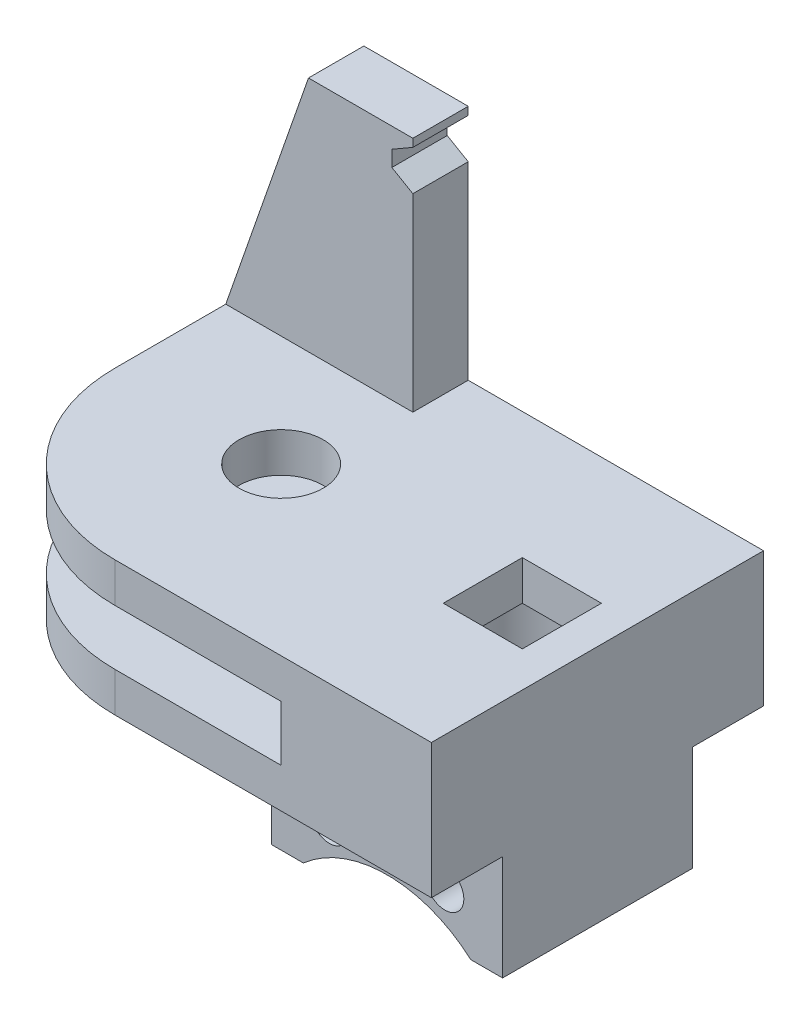
SolidWorks part; units mm, degrees
ref_plane "Front Plane" through (0, 0, 0) normal (0, 0, 1) x (1, 0, 0)
ref_plane "Top Plane" through (0, 0, 0) normal (0, 1, 0) x (1, 0, 0)
ref_plane "Right Plane" through (0, 0, 0) normal (1, 0, 0) x (0, 0, -1)
sketch "Sketch1" plane through (0, 0, 0) normal (0, 1, 0) x (1, 0, 0)
  line L0 (0, -13.335) -> (25.4, -13.335)
  line L1 (0, 13.335) -> (25.4, 13.335)
  line L2 (25.4, 13.335) -> (25.4, -13.335)
  circle A0 centre (0, 0) radius 12.7 construction
  circle A1 centre (0, 0) radius 13.335 construction
  circle A2 centre (0, 0) radius 3.3782
  arc A3 (11.5484, 6.6675) -> (11.5484, -6.6675) centre (0, 0) ccw construction
  arc A4 (0, 13.335) -> (0, -13.335) centre (0, 0) ccw
  dimension "D1" = 25.4
  dimension "D2" = 0.635
  dimension "D4" = 6.7564
  dimension "D3" = 25.4
extrude "Boss-Extrude1" add sketch "Sketch1" along normal blind 3.175
sketch "Sketch2" plane through (0, 0, 0) normal (0, -1, 0) x (-1, 0, 0)
  line L3 (-25.4, 13.335) -> (-25.4, -13.335)
  line L5 (-13.335, 0) -> (-13.335, 13.335)
  line L6 (-25.4, 13.335) -> (-13.335, 13.335)
  line L7 (-13.335, 0) -> (-13.335, -13.335)
  line L8 (0, -13.335) -> (-25.4, -13.335) construction
  line L9 (-13.335, -13.335) -> (-25.4, -13.335)
  arc A3 (0, 13.335) -> (0, -13.335) centre (0, 0) ccw construction
extrude "Boss-Extrude2" add sketch "Sketch2" along normal blind 4.445 contours L3 L9 L7 L5 L6
ref_plane "Plane2" through (0, -2.2225, 0) normal (0, -1, 0) x (-1, 0, 0)
mirror "Mirror2" about plane through (0, -2.2225, 0) normal (0, -1, 0) of "Boss-Extrude1"
sketch "Sketch7" plane through (0, -7.62, 0) normal (0, -1, 0) x (-1, 0, 0)
  line L0 (-25.4, 13.335) -> (-25.4, 7.62) construction
  line L1 (-25.4, 13.335) -> (-25.4, -13.335) construction
  line L2 (0, 0) -> (-25.4, 0) construction
  line L3 (-25.4, -13.335) -> (-25.4, -7.62) construction
  line L5 (-25.4, 7.62) -> (-6.858, 7.62)
  line L6 (-25.4, 7.62) -> (-25.4, -7.62)
  line L7 (-25.4, -7.62) -> (-6.858, -7.62)
  line L8 (-6.858, 7.62) -> (-6.858, -7.62)
  dimension "D1" = 5.715
  dimension "D2" = 18.542
extrude "Boss-Extrude4" add sketch "Sketch7" along normal blind 8.4391
sketch "Sketch8" plane through (0, 0, -7.62) normal (0, 0, -1) x (-1, 0, 0)
  line L0 (-16.129, -7.62) -> (-16.129, -16.0591) construction
  line L1 (-16.129, -16.0591) -> (-25.4, -16.0591) construction
  line L2 (-20.7645, -16.0591) -> (-20.7645, -7.62) construction
  line L3 (-6.858, -7.62) -> (-25.4, -7.62) construction
  line L4 (-6.858, -16.0591) -> (-25.4, -16.0591) construction
  line L5 (0, -7.62) -> (-25.4, -7.62) construction
  circle A0 centre (-20.7645, -12.1285) radius 1.524
  circle A1 centre (-11.4935, -12.1285) radius 1.524
  dimension "D1" = 3.048
  dimension "D2" = 4.5085
extrude "Cut-Extrude3" cut sketch "Sketch8" against normal through all
sketch "Sketch9" plane through (0, 0, -7.62) normal (0, 0, -1) x (-1, 0, 0)
  line L0 (-16.129, -16.0591) -> (-16.129, -23.6791) construction
  line L1 (-6.858, -16.0591) -> (-25.4, -16.0591) construction
  line L2 (-16.129, -16.0591) -> (-16.129, -13.5191) construction
  circle A0 centre (-16.129, -23.6791) radius 10.16
  dimension "D1" = 2.54
  dimension "D2" = 7.62
extrude "Cut-Extrude4" cut sketch "Sketch9" against normal through all
sketch "Sketch22" plane through (0, 3.175, 0) normal (0, 1, 0) x (1, 0, 0)
  line L0 (25.4, 0) -> (19.3675, 0) construction
  line L1 (25.4, 13.335) -> (25.4, -13.335) construction
  line L3 (16.1925, -3.175) -> (22.5425, -3.175)
  line L4 (16.1925, -3.175) -> (16.1925, 3.175)
  line L5 (16.1925, 3.175) -> (22.5425, 3.175)
  line L6 (22.5425, -3.175) -> (22.5425, 3.175)
  line L7 (16.1925, -3.175) -> (22.5425, 3.175) construction
  line L8 (16.1925, 3.175) -> (22.5425, -3.175) construction
  dimension "D1" = 6.0325
  dimension "D2" = 6.35
  dimension "D3" = 6.35
extrude "Cut-Extrude6" cut sketch "Sketch22" against normal blind 9.525
sketch "Sketch23" plane through (0, -6.35, 0) normal (0, 1, 0) x (1, 0, 0)
  line L0 (19.3675, 3.175) -> (19.3675, -3.175) construction
  line L1 (22.5425, 3.175) -> (16.1925, 3.175) construction
  line L2 (16.1925, -3.175) -> (22.5425, -3.175) construction
  circle A0 centre (19.3675, 0) radius 4.4901
extrude "Cut-Extrude7" cut sketch "Sketch23" along normal blind 6.35
sketch "Sketch16" plane through (0, 3.175, 0) normal (0, 1, 0) x (1, 0, 0)
  line L0 (0, 13.335) -> (-13.335, 0)
  line L1 (0, 13.335) -> (-13.335, 13.335)
  line L2 (0, 13.335) -> (0, 0) construction
  line L3 (0, 0) -> (-13.335, 0) construction
  line L4 (-13.335, 13.335) -> (-13.335, 0)
  arc A0 (0, 13.335) -> (0, -13.335) centre (0, 0) ccw construction
extrude "Boss-Extrude10" add sketch "Sketch16" against normal up to surface (3.175 mm away) up to face at (0, 0, 3.3782)
sketch "Sketch17" plane through (0, -7.62, 0) normal (0, -1, 0) x (1, 0, 0)
  line L0 (-13.335, -13.335) -> (-13.335, 0)
  line L1 (-13.335, 0) -> (0, -13.335)
  line L2 (0, -13.335) -> (-13.335, -13.335)
  arc A0 (0, 13.335) -> (0, -13.335) centre (0, 0) ccw construction
extrude "Boss-Extrude11" add sketch "Sketch17" against normal up to surface (3.175 mm away) up to face at (0, -4.445, 3.3782)
sketch "Sketch19" plane through (0, 3.175, 0) normal (0, 1, 0) x (1, 0, 0)
  line L0 (0, 0) -> (0, 13.335) construction
  line L1 (-13.335, 13.335) -> (25.4, 13.335) construction
  line L2 (3.3782, 0) -> (3.3782, 13.335) construction
  line L3 (3.3782, 13.335) -> (0, 13.335) construction
  line L5 (1.6891, 13.335) -> (-6.6929, 13.335)
  line L6 (1.6891, 13.335) -> (1.6891, 8.89)
  line L7 (1.6891, 8.89) -> (-6.6929, 8.89)
  line L8 (-6.6929, 13.335) -> (-6.6929, 8.89)
  circle A0 centre (0, 0) radius 3.3782 construction
  dimension "D1" = 8.382
  dimension "D2" = 4.445
extrude "Boss-Extrude12" add sketch "Sketch19" along normal blind 19.05
sketch "Sketch20" plane through (0, 0, -8.89) normal (0, 0, 1) x (1, 0, 0)
  line L0 (-6.6929, 22.225) -> (-13.335, 3.175)
  line L1 (-13.335, 3.175) -> (-6.6929, 3.175)
  line L2 (-6.6929, 3.175) -> (-6.6929, 22.225)
extrude "Boss-Extrude13" add sketch "Sketch20" against normal up to surface (4.445 mm away) up to face at (1.1769, 2.7517, -13.335)
sketch "Sketch21" plane through (0, 0, -8.89) normal (0, 0, 1) x (1, 0, 0)
  line L0 (0, 3.175) -> (0, 22.225) construction
  line L1 (3.3782, 3.175) -> (-3.3782, 3.175) construction
  line L2 (-6.6929, 22.225) -> (1.6891, 22.225) construction
  line L3 (0, 20.6148) -> (1.6891, 21.59)
  line L4 (1.6891, 22.225) -> (1.6891, 3.175) construction
  line L5 (1.6891, 21.59) -> (1.6891, 18.3696)
  line L7 (0, 20.6148) -> (0, 19.3448)
  line L8 (0, 19.3448) -> (1.6891, 18.3696)
  dimension "D1" = 60
  dimension "D2" = 60
  dimension "D3" = 0.635
  dimension "D4" = 1.27
extrude "Cut-Extrude5" cut sketch "Sketch21" against normal blind 12.7
